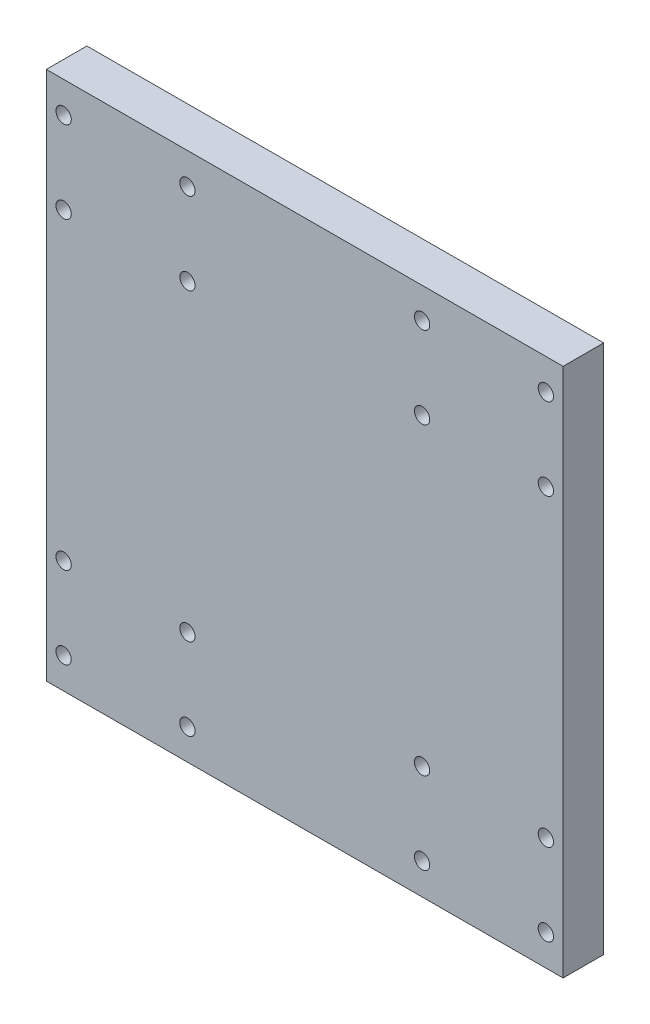
SolidWorks part; units mm, degrees
ref_plane "Front Plane" through (0, 0, 0) normal (0, 0, 1) x (1, 0, 0)
ref_plane "Top Plane" through (0, 0, 0) normal (0, 1, 0) x (1, 0, 0)
ref_plane "Right Plane" through (0, 0, 0) normal (1, 0, 0) x (0, 0, -1)
sketch "Sketch1" plane through (0, 0, 0) normal (0, 0, 1) x (1, 0, 0)
  line L0 (68.4396, -10.2242) -> (68.4396, 68.1282)
  line L1 (68.4396, 68.1282) -> (-8.0026, 67.9392)
  line L2 (-8.0026, 67.9392) -> (-8.0026, -10.4131)
  line L3 (-8.0026, -10.4131) -> (68.4396, -10.2242)
  line L4 (45.0166, -10.2242) -> (45.0166, 11.045) construction
  line L5 (45.0166, 11.045) -> (68.4396, 11.045) construction
  line L6 (15.4204, -10.4131) -> (15.4204, 10.8561) construction
  line L7 (-8.0026, 10.8561) -> (15.4204, 10.8561) construction
  line L8 (68.4396, 46.859) -> (45.0166, 46.859) construction
  line L9 (45.0166, 46.859) -> (45.0166, 68.1282) construction
  line L10 (15.4204, 67.9392) -> (15.4204, 46.6701) construction
  line L11 (15.4204, 46.6701) -> (-8.0026, 46.6701) construction
  circle A0 centre (-5.4449, -5.8335) radius 1.1321
  circle A1 centre (-5.4449, 6.2818) radius 1.1321
  circle A2 centre (12.8627, 6.2818) radius 1.1321
  circle A3 centre (12.8627, -5.8335) radius 1.1321
  circle A4 centre (47.5743, -5.6499) radius 1.1321
  circle A5 centre (47.5743, 6.4654) radius 1.1321
  circle A6 centre (65.8819, 6.4654) radius 1.1321
  circle A7 centre (65.8819, -5.6499) radius 1.1321
  circle A8 centre (47.5743, 51.4332) radius 1.1321
  circle A9 centre (47.5743, 63.5486) radius 1.1321
  circle A10 centre (65.8819, 63.5486) radius 1.1321
  circle A11 centre (65.8819, 51.4332) radius 1.1321
  circle A12 centre (12.8627, 51.2497) radius 1.1321
  circle A13 centre (12.8627, 63.365) radius 1.1321
  circle A14 centre (-5.4449, 63.365) radius 1.1321
  circle A15 centre (-5.4449, 51.2497) radius 1.1321
  point P80 (0, 0)
extrude "Boss-Extrude1" add sketch "Sketch1" along normal blind 5.9944 contours L1 L2 L3 L0
